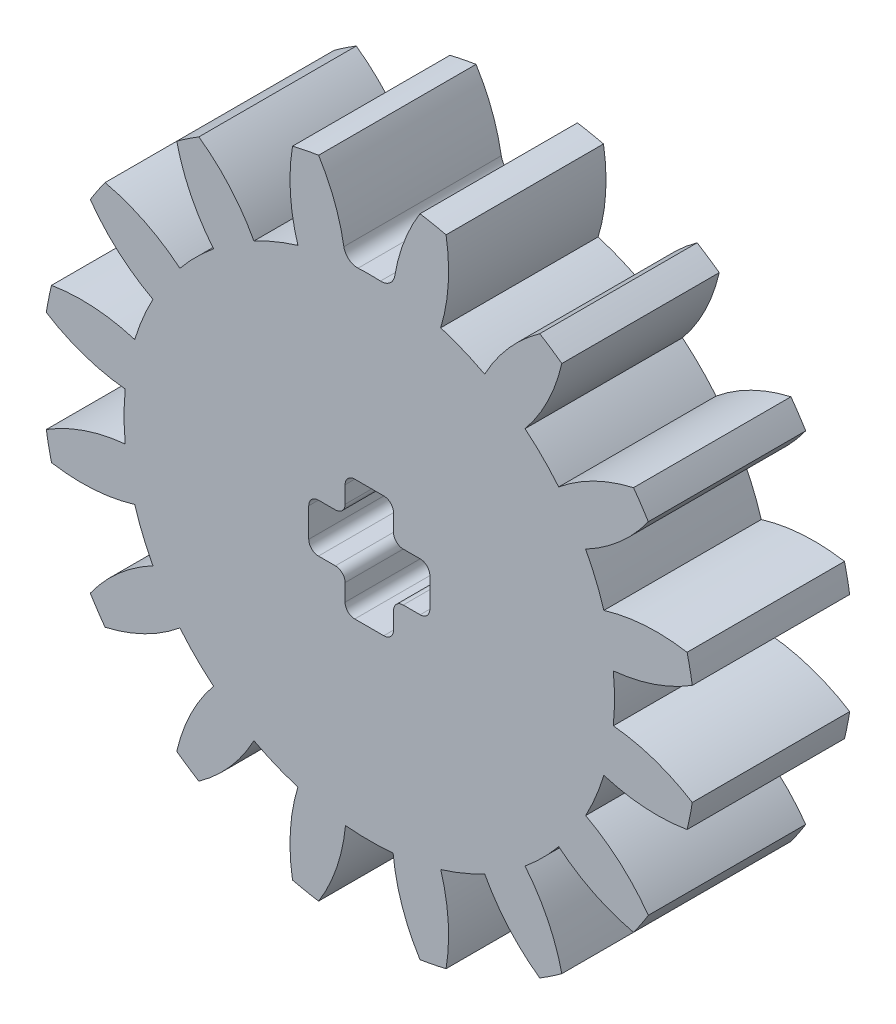
SolidWorks part; units mm, degrees
ref_plane "Front Plane" through (0, 0, 0) normal (0, 0, 1) x (1, 0, 0)
ref_plane "Top Plane" through (0, 0, 0) normal (0, 1, 0) x (1, 0, 0)
ref_plane "Right Plane" through (0, 0, 0) normal (1, 0, 0) x (0, 0, -1)
sketch "Sketch1" plane through (0, 0, 0) normal (0, 0, 1) x (1, 0, 0)
  line L0 (1.4, 1) -> (2.1, 1)
  line L3 (-0.6, 2.5) -> (0.6, 2.5)
  line L6 (-1, 2.1) -> (-1, 1.4)
  line L7 (-0.6, -2.5) -> (0.6, -2.5)
  line L8 (1, 2.1) -> (1, 1.4)
  line L9 (-1, 2.5) -> (1, -2.5) construction
  line L10 (-1, -2.5) -> (1, 2.5) construction
  line L11 (-2.1, 1) -> (-1.4, 1)
  line L12 (-2.5, 0.6) -> (-2.5, -0.6)
  line L13 (-2.1, -1) -> (-1.4, -1)
  line L14 (2.5, 0.6) -> (2.5, -0.6)
  line L15 (-2.5, 1) -> (2.5, -1) construction
  line L16 (-2.5, -1) -> (2.5, 1) construction
  line L17 (1, -1.4) -> (1, -2.1)
  line L18 (1.4, -1) -> (2.1, -1)
  line L19 (-1, -1.4) -> (-1, -2.1)
  circle A0 centre (0, 0) radius 13.5
  arc A1 (-1.4, 1) -> (-1, 1.4) centre (-1.4, 1.4) ccw
  arc A2 (-2.1, 1) -> (-2.5, 0.6) centre (-2.1, 0.6) ccw
  arc A3 (-2.5, -0.6) -> (-2.1, -1) centre (-2.1, -0.6) ccw
  arc A4 (-1.4, -1) -> (-1, -1.4) centre (-1.4, -1.4) cw
  arc A5 (-1, -2.1) -> (-0.6, -2.5) centre (-0.6, -2.1) ccw
  arc A6 (0.6, -2.5) -> (1, -2.1) centre (0.6, -2.1) ccw
  arc A7 (1, -1.4) -> (1.4, -1) centre (1.4, -1.4) cw
  arc A8 (2.1, -1) -> (2.5, -0.6) centre (2.1, -0.6) ccw
  arc A9 (2.1, 1) -> (2.5, 0.6) centre (2.1, 0.6) cw
  arc A10 (1.4, 1) -> (1, 1.4) centre (1.4, 1.4) cw
  arc A11 (0.6, 2.5) -> (1, 2.1) centre (0.6, 2.1) cw
  arc A12 (-0.6, 2.5) -> (-1, 2.1) centre (-0.6, 2.1) ccw
  point P7 (0, 0)
  point P13 (0, 0)
  point P27 (-1, -1)
  point P36 (1, -1)
  dimension "D2" = 27
  dimension "D4" = 0.4
  dimension "D1" = 5
extrude "Boss-Extrude1" add sketch "Sketch1" along normal mid plane 6.5
sketch "Sketch2" plane through (0, 0, 0) normal (0, 0, 1) x (1, 0, 0)
  line L0 (0, 0) -> (0, 13.5) construction
  line L1 (0, 0) -> (-0.9822, 10.0772) construction
  line L2 (0, 8.0719) -> (-4.2467, 19.7397) construction
  arc A0 (1.3999, 11.9181) -> (-1.3999, 11.9181) centre (0, 0) ccw construction
  arc A1 (0.9822, 10.0772) -> (-0.9822, 10.0772) centre (0, 0) ccw
  arc A3 (2.0928, 13.3368) -> (-2.0928, 13.3368) centre (0, 0) ccw
  arc A4 (-0.9822, 10.0772) -> (-2.0928, 13.3368) centre (-8.4601, 9.3484) ccw
  arc A5 (0.9822, 10.0772) -> (2.0928, 13.3368) centre (8.4601, 9.3484) cw
  circle A6 centre (0, 0) radius 13.5 construction
  dimension "D1" = 24
  dimension "D2" = 3.375
  dimension "D3" = 20
  dimension "D4" = 2.8062
extrude "Cut-Extrude1" cut sketch "Sketch2" against normal through all both and the other way through all
fillet "Fillet1" radius 0.57 2 edges at (0.9822, 10.0772, 0) (-0.9822, 10.0772, 0)
pattern_circular "CirPattern3" count 16 over 360 about axis through (0, 0, 0) along (0, 0, 1) of "Cut-Extrude1"
equation "\"Module\"= 1.5"
equation "\"Pressure Angle\"= 20"
equation "\"Bore\"= 2"
equation "\"NumTeeth\"= 16"
equation "\"D2@Sketch1\"=(\"NumTeeth\"+2)*\"Module\""
equation "\"D1@Sketch2\"=\"NumTeeth\"*\"Module\""
equation "\"ToothDepth\"= IIF ( \"Module\" < 1.25 , 2.4 * \"Module\" , 2.25 * \"Module\" )"
equation "\"D2@Sketch2\"=\"ToothDepth\""
equation "\"D3@Sketch2\"=\"Pressure Angle\""
equation "\"D4@Sketch2\"=((\"Module\"*PI)/2)+0.3*\"Module\""
equation "\"D1@Fillet1\"=\"Module\"*0.38"
equation "\"D1@CirPattern3\"=\"NumTeeth\""
